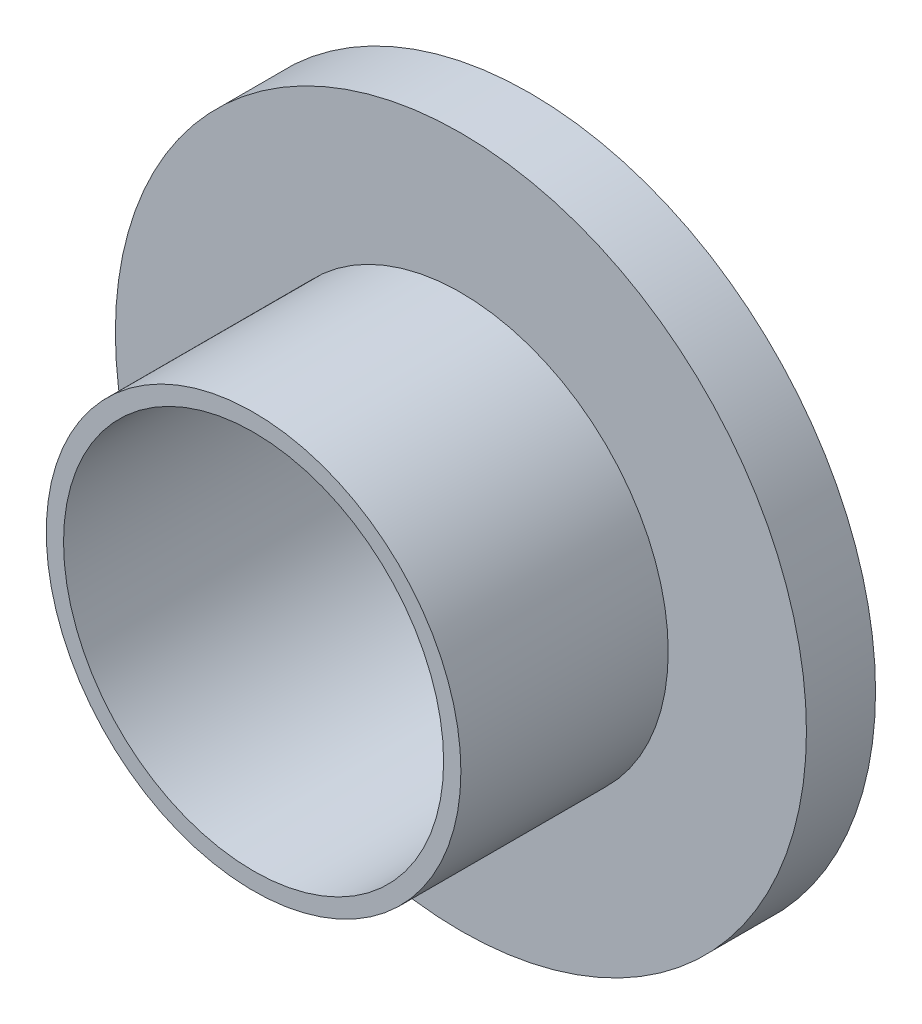
SolidWorks part; units mm, degrees
ref_plane "Plan de face" through (0, 0, 0) normal (0, 0, 1) x (1, 0, 0)
ref_plane "Plan de dessus" through (0, 0, 0) normal (0, 1, 0) x (1, 0, 0)
ref_plane "Plan de droite" through (0, 0, 0) normal (1, 0, 0) x (0, 0, -1)
sketch "Esquisse1" plane through (0, 0, 0) normal (0, 0, 1) x (1, 0, 0)
  circle A0 centre (0, 0) radius 20
  dimension "D1" = 40
extrude "Boss.-Extru.1" add sketch "Esquisse1" along normal blind 16
sketch "Esquisse2" plane through (0, 0, 16) normal (0, 0, 1) x (1, 0, 0)
  circle A0 centre (0, 0) radius 12
  circle A1 centre (0, 0) radius 20
  dimension "D1" = 24
extrude "Enlèv. mat.-Extru.1" cut sketch "Esquisse2" against normal blind 12
sketch "Esquisse3" plane through (0, 0, 16) normal (0, 0, 1) x (1, 0, 0)
  circle A0 centre (0, 0) radius 11
  dimension "D1" = 22
extrude "Enlèv. mat.-Extru.2" cut sketch "Esquisse3" against normal through all
